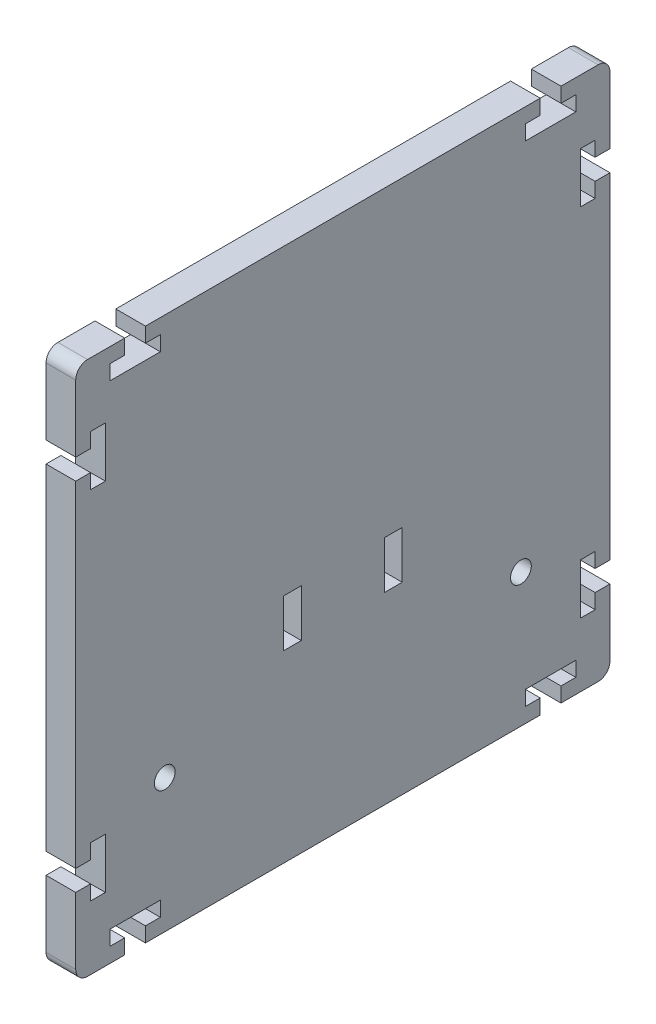
SolidWorks part; units mm, degrees
ref_plane "Спереди" through (0, 0, 0) normal (0, 0, 1) x (1, 0, 0)
ref_plane "Сверху" through (0, 0, 0) normal (0, 1, 0) x (1, 0, 0)
ref_plane "Справа" through (0, 0, 0) normal (1, 0, 0) x (0, 0, -1)
sketch "Эскиз1" plane through (0, 0, 0) normal (1, 0, 0) x (0, 0, -1)
  line L0 (-36.75, 45) -> (-36.75, 42.5)
  line L1 (-43, -45) -> (-36.75, -45)
  line L2 (-45, -43) -> (-45, -31.75)
  line L3 (-43, 45) -> (-36.75, 45)
  line L4 (45, -43) -> (45, -31.75)
  line L5 (-45, -45) -> (45, 45) construction
  line L6 (-45, 45) -> (45, -45) construction
  line L7 (-36.75, 42.5) -> (-39.25, 42.5)
  line L8 (-39.25, 42.5) -> (-39.25, 40)
  line L9 (-39.25, 40) -> (-30.75, 40)
  line L10 (-33.25, 45) -> (33.25, 45)
  line L11 (-30.75, 42.5) -> (-30.75, 40)
  line L12 (-33.25, 42.5) -> (-30.75, 42.5)
  line L13 (-33.25, 45) -> (-33.25, 42.5)
  line L14 (0, 0) -> (0, 21.2721) construction
  line L15 (0, 0) -> (18.8007, 0) construction
  line L16 (33.25, 45) -> (33.25, 42.5)
  line L17 (33.25, 42.5) -> (30.75, 42.5)
  line L18 (30.75, 42.5) -> (30.75, 40)
  line L19 (39.25, 40) -> (30.75, 40)
  line L20 (39.25, 42.5) -> (39.25, 40)
  line L21 (36.75, 42.5) -> (39.25, 42.5)
  line L22 (36.75, 45) -> (36.75, 42.5)
  line L23 (-33.25, -45) -> (-33.25, -42.5)
  line L24 (-33.25, -42.5) -> (-30.75, -42.5)
  line L25 (-30.75, -42.5) -> (-30.75, -40)
  line L26 (-39.25, -40) -> (-30.75, -40)
  line L27 (-39.25, -42.5) -> (-39.25, -40)
  line L28 (-36.75, -42.5) -> (-39.25, -42.5)
  line L29 (-36.75, -45) -> (-36.75, -42.5)
  line L30 (36.75, -45) -> (36.75, -42.5)
  line L31 (36.75, -42.5) -> (39.25, -42.5)
  line L32 (39.25, -42.5) -> (39.25, -40)
  line L33 (39.25, -40) -> (30.75, -40)
  line L34 (30.75, -42.5) -> (30.75, -40)
  line L35 (33.25, -42.5) -> (30.75, -42.5)
  line L36 (33.25, -45) -> (33.25, -42.5)
  line L37 (36.75, 45) -> (43, 45)
  line L38 (36.75, -45) -> (43, -45)
  line L39 (-33.25, -45) -> (33.25, -45)
  line L40 (-42.5, 28.25) -> (-42.5, 25.75)
  line L41 (-42.5, 34.25) -> (-40, 34.25)
  line L42 (-42.5, 34.25) -> (-42.5, 31.75)
  line L43 (-42.5, 25.75) -> (-40, 25.75)
  line L44 (-40, 34.25) -> (-40, 25.75)
  line L45 (-42.5, 31.75) -> (-45, 31.75)
  line L46 (-45, -45) -> (45, 45) construction
  line L47 (-42.5, 28.25) -> (-45, 28.25)
  line L48 (-45, 45) -> (45, -45) construction
  line L49 (-45, 31.75) -> (-45, 43)
  line L50 (0, 0) -> (0, 21.2721) construction
  line L51 (0, 0) -> (18.8007, 0) construction
  line L52 (-50, -45) -> (50, 45) construction
  line L53 (-50, 45) -> (50, -45) construction
  line L54 (0, 0) -> (0, 21.2721) construction
  line L55 (-13, -23) -> (13, 3) construction
  line L56 (13, 3) -> (13, -23) construction
  line L57 (13, -23) -> (-13, -23) construction
  line L58 (-13, 3) -> (-13, -23) construction
  line L59 (13, -23) -> (-13, 3) construction
  line L60 (0, -10) -> (0, -23) construction
  line L61 (0, -10) -> (-8.5, -10) construction
  line L62 (-42.5, -28.25) -> (-45, -28.25)
  line L63 (-42.5, -31.75) -> (-45, -31.75)
  line L64 (-40, -34.25) -> (-40, -25.75)
  line L65 (-42.5, -25.75) -> (-40, -25.75)
  line L66 (-42.5, -34.25) -> (-42.5, -31.75)
  line L67 (-42.5, -34.25) -> (-40, -34.25)
  line L68 (-42.5, -28.25) -> (-42.5, -25.75)
  line L69 (42.5, -28.25) -> (42.5, -25.75)
  line L70 (42.5, -34.25) -> (40, -34.25)
  line L71 (42.5, -34.25) -> (42.5, -31.75)
  line L72 (42.5, -25.75) -> (40, -25.75)
  line L73 (40, -34.25) -> (40, -25.75)
  line L74 (42.5, -31.75) -> (45, -31.75)
  line L75 (42.5, -28.25) -> (45, -28.25)
  line L76 (42.5, 28.25) -> (45, 28.25)
  line L77 (42.5, 31.75) -> (45, 31.75)
  line L78 (40, 34.25) -> (40, 25.75)
  line L79 (42.5, 25.75) -> (40, 25.75)
  line L80 (42.5, 34.25) -> (42.5, 31.75)
  line L81 (42.5, 34.25) -> (40, 34.25)
  line L82 (42.5, 28.25) -> (42.5, 25.75)
  line L83 (-45, -28.25) -> (-45, 28.25)
  line L84 (45, -28.25) -> (45, 28.25)
  line L85 (45, 31.75) -> (45, 43)
  line L86 (10, -6) -> (7, -6)
  line L87 (-10, -14) -> (-7, -14)
  line L88 (-10, -14) -> (-10, -6)
  line L89 (-10, -6) -> (-7, -6)
  line L90 (-7, -14) -> (-7, -6)
  line L91 (-10, -14) -> (-7, -6) construction
  line L92 (-10, -6) -> (-7, -14) construction
  line L93 (10, -14) -> (7, -14)
  line L94 (10, -14) -> (10, -6)
  line L95 (7, -14) -> (7, -6)
  arc A0 (43, 45) -> (45, 43) centre (43, 43) cw
  arc A1 (45, -43) -> (43, -45) centre (43, -43) cw
  arc A2 (-45, -43) -> (-43, -45) centre (-43, -43) ccw
  arc A3 (-43, 45) -> (-45, 43) centre (-43, 43) ccw
  circle A4 centre (-30, -22.5) radius 1.75
  circle A5 centre (30, -22.5) radius 1.75
  point P0 (0, 0)
  point P16 (-37, 42.5)
  point P27 (37, 42.5)
  point P36 (-37, -42.5)
  point P45 (37, -42.5)
  point P89 (0, 0)
  dimension "D10" = 13.25
  dimension "D16" = 2
  dimension "D17" = 2
  dimension "D21" = 3.5
  dimension "D1" = 90
  dimension "D2" = 90
  dimension "D3" = 3.5
  dimension "D4" = 8.25
  dimension "D5" = 2.5
  dimension "D6" = 2.5
  dimension "D7" = 5
  dimension "D8" = 2.5
  dimension "D9" = 8.5
  dimension "D11" = 3.5
  dimension "D12" = 2.5
  dimension "D13" = 8.5
  dimension "D14" = 2.5
  dimension "D15" = 2.5
  dimension "D18" = 8.5
  dimension "D19" = 3
  dimension "D20" = 8
  dimension "D22" = 67.5
  dimension "D23" = 51
extrude "Бобышка-Вытянуть1" add sketch "Эскиз1" along normal blind 5
